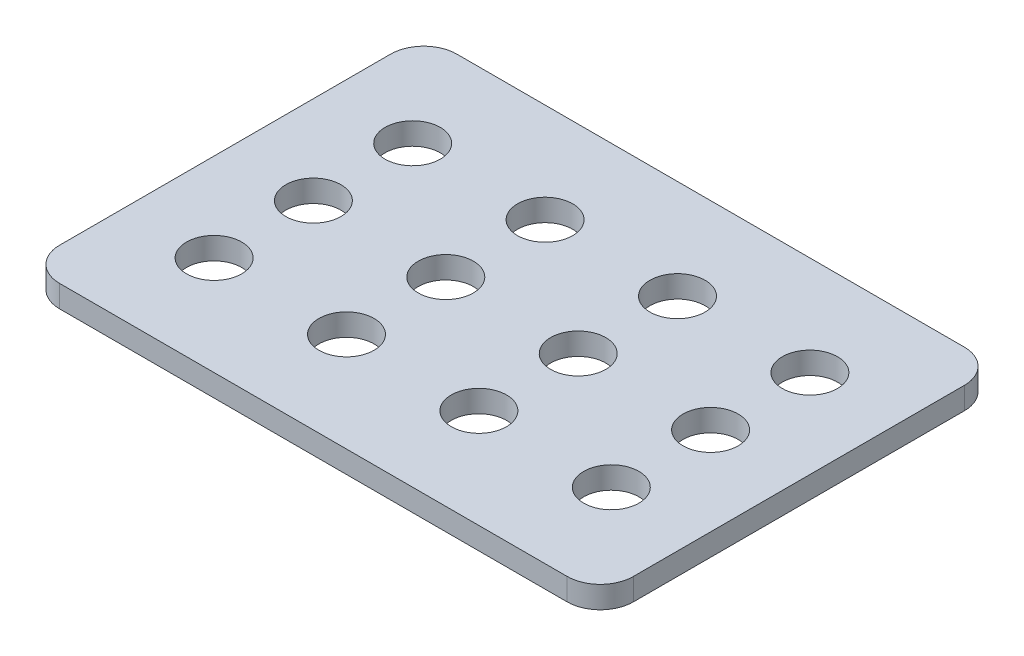
SolidWorks part; units mm, degrees
ref_plane "Front Plane" through (0, 0, 0) normal (0, 0, 1) x (1, 0, 0)
ref_plane "Top Plane" through (0, 0, 0) normal (0, 1, 0) x (1, 0, 0)
ref_plane "Right Plane" through (0, 0, 0) normal (1, 0, 0) x (0, 0, -1)
sketch "Sketch1" plane through (0, 0, 0) normal (0, 1, 0) x (1, 0, 0)
  line L1 (-115, 90) -> (115, 90)
  line L2 (-130, 75) -> (-130, -75)
  line L3 (-115, -90) -> (115, -90)
  line L4 (130, 75) -> (130, -75)
  line L5 (-130, 90) -> (130, -90) construction
  line L6 (-130, -90) -> (130, 90) construction
  arc A0 (115, 90) -> (130, 75) centre (115, 75) cw
  arc A1 (-130, -75) -> (-115, -90) centre (-115, -75) ccw
  arc A2 (-115, 90) -> (-130, 75) centre (-115, 75) ccw
  arc A3 (115, -90) -> (130, -75) centre (115, -75) ccw
  circle A4 centre (-90, -45) radius 12.5
  circle A5 centre (-30, -45) radius 12.5
  circle A6 centre (30, -45) radius 12.5
  circle A7 centre (90, -45) radius 12.5
  circle A8 centre (-30, 0) radius 12.5
  circle A9 centre (30, 0) radius 12.5
  circle A10 centre (90, 0) radius 12.5
  circle A11 centre (-30, 45) radius 12.5
  circle A12 centre (30, 45) radius 12.5
  circle A13 centre (90, 45) radius 12.5
  circle A14 centre (-90, 0) radius 12.5
  circle A15 centre (-90, 45) radius 12.5
  point P0 (0, 0)
  point P20 (0, 0)
  point P21 (0, 0)
  dimension "D3" = 15
  dimension "D4" = 25
  dimension "D1" = 180
  dimension "D2" = 260
  dimension "D5" = 45
  dimension "D6" = 40
  dimension "D7" = 4
  dimension "D8" = 3
extrude "Boss-Extrude1" add sketch "Sketch1" along normal blind 10
